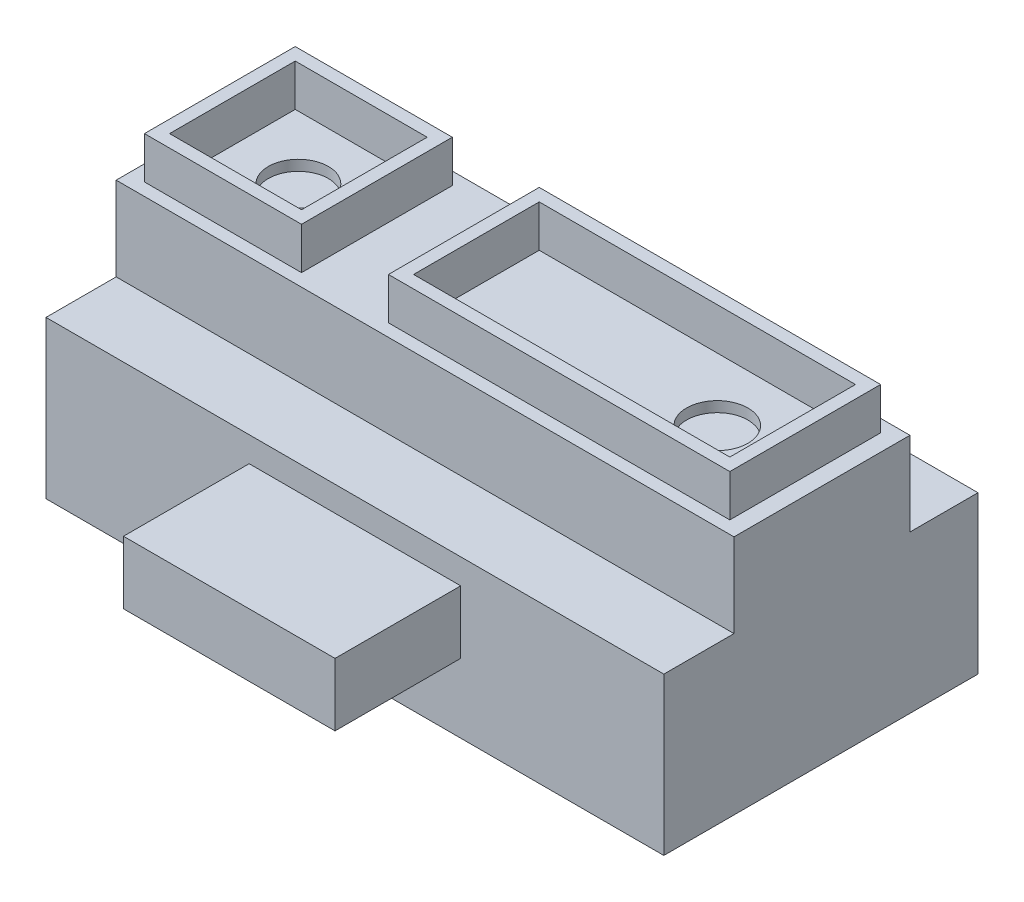
SolidWorks part; units mm, degrees
material "PE niedrige/mittlere Dichte"
ref_plane "Vorne" through (0, 0, 0) normal (0, 0, 1) x (1, 0, 0)
ref_plane "Oben" through (0, 0, 0) normal (0, 1, 0) x (1, 0, 0)
ref_plane "Rechts" through (0, 0, 0) normal (1, 0, 0) x (0, 0, -1)
sketch "Skizze2" plane through (0, 0, 0) normal (0, 1, 0) x (1, 0, 0)
  line L1 (0, 0) -> (29.5, 0)
  line L2 (0, 0) -> (0, 15)
  line L3 (0, 15) -> (29.5, 15)
  line L4 (29.5, 0) -> (29.5, 15)
  dimension "D1" = 29.5
  dimension "D2" = 15
extrude "Aufsatz-Linear austragen1" add sketch "Skizze2" along normal blind 7.5
sketch "Skizze4" plane through (0, 0, 0) normal (0, -1, 0) x (1, 0, 0)
  line L8 (0.8, -0.8) -> (0.8, -14.2)
  line L9 (0.8, -14.2) -> (28.7, -14.2)
  line L10 (28.7, -14.2) -> (28.7, -0.8)
  line L11 (28.7, -0.8) -> (0.8, -0.8)
  line L12 (0.8, -0.8) -> (0.8, -14.2)
  line L13 (0.8, -14.2) -> (28.7, -14.2)
  line L14 (28.7, -14.2) -> (28.7, -0.8)
  line L15 (28.7, -0.8) -> (0.8, -0.8)
  dimension "D1" = 0.8
extrude "Schnitt-Linear austragen1" cut sketch "Skizze4" against normal blind 5.7
sketch "Skizze5" plane through (0, 7.5, 0) normal (0, 1, 0) x (1, 0, 0)
  line L0 (0, 15) -> (0, 0) construction
  line L2 (29.5, 0) -> (29.5, 15) construction
  line L4 (0, 3.35) -> (29.5, 3.35)
  line L5 (29.5, 3.35) -> (29.5, 11.75)
  line L6 (29.5, 11.75) -> (0, 11.75)
  line L7 (0, 11.75) -> (0, 3.35)
  line L8 (29.5, 15) -> (0, 15) construction
  dimension "D1" = 8.4
  dimension "D2" = 3.25
extrude "Aufsatz-Linear austragen2" add sketch "Skizze5" along normal blind 4
sketch "Skizze7" plane through (0, 11.5, 0) normal (0, 1, 0) x (1, 0, 0)
  line L0 (1.35, 4.55) -> (7.65, 4.55)
  line L1 (0.75, 3.95) -> (8.25, 3.95)
  line L2 (0.75, 3.95) -> (0.75, 11.15)
  line L3 (0.75, 11.15) -> (8.25, 11.15)
  line L4 (8.25, 3.95) -> (8.25, 11.15)
  line L5 (12.4, 3.95) -> (28.7, 3.95)
  line L6 (12.4, 3.95) -> (12.4, 11.15)
  line L7 (12.4, 11.15) -> (28.7, 11.15)
  line L8 (28.7, 3.95) -> (28.7, 11.15)
  line L9 (7.65, 4.55) -> (7.65, 10.55)
  line L10 (0, -6.325) -> (0, 6.325) construction
  line L11 (0, 3.35) -> (29.5, 3.35) construction
  line L12 (1.35, 10.55) -> (7.65, 10.55)
  line L13 (1.35, 4.55) -> (1.35, 10.55)
  line L14 (13, 4.55) -> (13, 10.55)
  line L15 (13, 10.55) -> (28.1, 10.55)
  line L16 (28.1, 4.55) -> (28.1, 10.55)
  line L17 (13, 4.55) -> (28.1, 4.55)
  dimension "D1" = 7.5
  dimension "D2" = 4.15
  dimension "D3" = 16.3
  dimension "D4" = 0.75
  dimension "D5" = 7.2
  dimension "D6" = 0.6
  dimension "D7" = 0.6
  dimension "D8" = 0.6
extrude "Aufsatz-Linear austragen3" add sketch "Skizze7" along normal blind 2 contours L1 L4 L3 L2 L0 L13 L12 L9 | L5 L8 L7 L6 L17 L14 L15 L16
sketch "Skizze8" plane through (0, 11.5, 0) normal (0, 1, 0) x (-1, 0, 0)
  line L0 (-1.35, -7.55) -> (-29.5, -7.55) construction
  line L1 (-1.35, -4.55) -> (-1.35, -10.55) construction
  line L2 (-29.5, -3.35) -> (-29.5, -11.75) construction
  line L3 (-0.75, -3.95) -> (-0.75, -11.15) construction
  circle A0 centre (-4.5, -7.55) radius 1.4341
  circle A1 centre (-24.5, -7.55) radius 1.4634
  dimension "D1" = 3.75
  dimension "D2" = 20
extrude "Schnitt-Linear austragen2" cut sketch "Skizze8" against normal blind 0.5
sketch "Skizze9" plane through (0, 0, 0) normal (0, 0, 1) x (1, 0, 0)
  line L0 (8.25, 0) -> (-8.25, 0) construction
  line L1 (9.7, 6.3) -> (19.8, 6.3)
  line L2 (9.7, 6.3) -> (9.7, 3.3)
  line L3 (9.7, 3.3) -> (19.8, 3.3)
  line L4 (19.8, 6.3) -> (19.8, 3.3)
  line L5 (0, 7.5) -> (0, 0) construction
  dimension "D1" = 10.1
  dimension "D2" = 3.3
  dimension "D3" = 9.7
  dimension "D4" = 3
extrude "Aufsatz-Linear austragen4" add sketch "Skizze9" along normal blind 6
